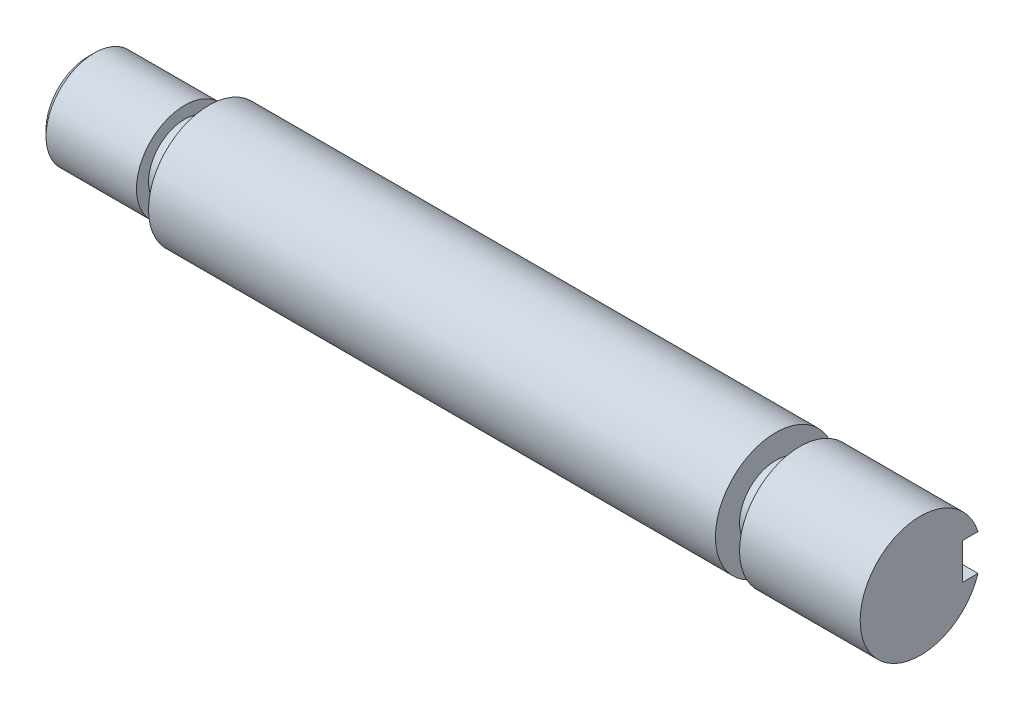
SolidWorks part; units mm, degrees
ref_plane "Front Plane" through (0, 0, 0) normal (0, 0, 1) x (1, 0, 0)
ref_plane "Top Plane" through (0, 0, 0) normal (0, 1, 0) x (1, 0, 0)
ref_plane "Right Plane" through (0, 0, 0) normal (1, 0, 0) x (0, 0, -1)
sketch "Sketch1" plane through (0, 0, 0) normal (1, 0, 0) x (0, 0, -1)
  circle A0 centre (0, 0) radius 5
  dimension "D1" = 10
extrude "Boss-Extrude1" add sketch "Sketch1" along normal mid plane 69
sketch "Sketch2" plane through (34.5, 0, 0) normal (1, 0, 0) x (0, 0, -1)
  circle A0 centre (0, 0) radius 3
  circle A1 centre (0, 0) radius 5
  circle A2 centre (0, 0) radius 5
  dimension "D1" = 0
extrude "Cut-Extrude1" cut sketch "Sketch2" against normal blind 2 from offset 10 offset against normal yes
sketch "Sketch3" plane through (0, 0, 0) normal (0, 0, 1) x (1, 0, 0)
  line L1 (34.5, 0) -> (9, 0) construction
  line L2 (34.5, -5) -> (34.5, 5) construction
  line L3 (68.4229, -1.5) -> (9, -1.5)
  line L4 (68.4229, 1.5) -> (9, 1.5)
  line L5 (68.4229, 1.5) -> (68.4229, -1.5)
  arc A1 (9, 1.5) -> (9, -1.5) centre (9, 0) ccw
  point P0 (4.7886, 0)
  dimension "D1" = 1.5
extrude "Cut-Extrude4" cut sketch "Sketch3" against normal blind 3.2 from offset 3.5 offset against normal yes
chamfer "Chamfer1" distance 0.5 angle 45 1 edges at (-34.5, 0, -5)
sketch "Sketch4" plane through (-34.5, 0, 0) normal (-1, 0, 0) x (0, 0, 1)
  circle A0 centre (0, 0) radius 4
extrude "Cut-Extrude5" cut sketch "Sketch4" against normal blind 8 flip side to cut
chamfer "Chamfer2" distance 0.5 angle 45 1 edges at (-34.5, 0, 4)
sketch "Sketch5" plane through (-26.5, 0, 0) normal (-1, 0, 0) x (0, 0, 1)
  circle A0 centre (0, 0) radius 4 construction
  circle A1 centre (0, 0) radius 5
  circle A2 centre (0, 0) radius 5
  circle A3 centre (0, 0) radius 4
  dimension "D1" = 0
sketch "Sketch6" plane through (-34.5, 0, 0) normal (-1, 0, 0) x (0, 0, 1)
  circle A0 centre (0, 0) radius 3
extrude "Cut-Extrude6" cut sketch "Sketch6" against normal blind 2 from offset 8 flip side to cut
